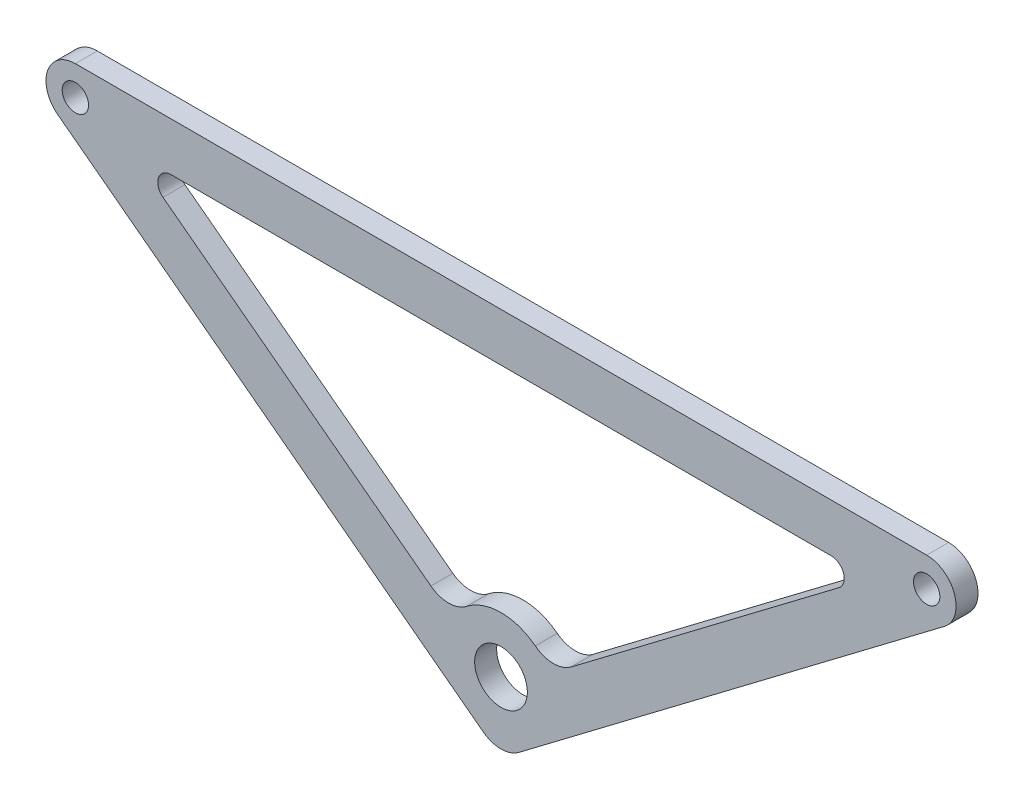
SolidWorks part; units mm, degrees
ref_plane "Front Plane" through (0, 0, 0) normal (0, 0, 1) x (1, 0, 0)
ref_plane "Top Plane" through (0, 0, 0) normal (0, 1, 0) x (1, 0, 0)
ref_plane "Right Plane" through (0, 0, 0) normal (1, 0, 0) x (0, 0, -1)
sketch "Sketch1" plane through (0, 0, 0) normal (0, 0, 1) x (1, 0, 0)
  line L2 (96.9091, 0) -> (-96.9091, 0)
  line L3 (-96.9091, -6.6956) -> (0, -80) construction
  line L5 (-100.9484, -12.0356) -> (-4.0393, -85.34)
  line L6 (-76.9545, -16.3926) -> (-15.9714, -62.5217)
  line L7 (0, -80) -> (96.9091, -6.6956) construction
  line L9 (4.0393, -85.34) -> (100.9484, -12.0356)
  line L10 (75.1447, -11) -> (-75.1447, -11)
  line L11 (15.9714, -62.5217) -> (76.9545, -16.3926)
  circle A2 centre (96.9091, -6.6956) radius 3
  circle A3 centre (-96.9091, -6.6956) radius 3
  arc A4 (-96.9091, 0) -> (-100.9484, -12.0356) centre (-96.9091, -6.6956) ccw
  arc A5 (-4.0393, -85.34) -> (4.0393, -85.34) centre (0, -80) ccw
  arc A9 (96.9091, 0) -> (100.9484, -12.0356) centre (96.9091, -6.6956) cw
  arc A10 (-7.8095, -62.4618) -> (7.8095, -62.4618) centre (0, -72.4768) cw
  circle A11 centre (0, -72.4768) radius 6
  arc A12 (-7.8095, -62.4618) -> (-15.9714, -62.5217) centre (-11.9295, -57.1782) cw
  arc A13 (7.8095, -62.4618) -> (15.9714, -62.5217) centre (11.9295, -57.1782) ccw
  arc A14 (75.1447, -11) -> (76.9545, -16.3926) centre (75.1447, -14) cw
  arc A15 (-75.1447, -11) -> (-76.9545, -16.3926) centre (-75.1447, -14) ccw
  point P5 (55, -30.9523)
  point P12 (-55, -30.9523)
  dimension "D3" = 6
  dimension "D7" = 6.6956
  dimension "D13" = 12.7
  dimension "D14" = 12
  dimension "D15" = 3
  dimension "D4" = 6.7
  dimension "D2" = 11
  dimension "D5" = 11
  dimension "D6" = 80
  dimension "D8" = 4.0393
  dimension "D9" = 55
  dimension "D10" = 55
  dimension "D11" = 30.9523
  dimension "D12" = 30.9523
  dimension "D16" = 7.8095
  dimension "D17" = 15.9714
extrude "Boss-Extrude1" add sketch "Sketch1" along normal mid plane 5
